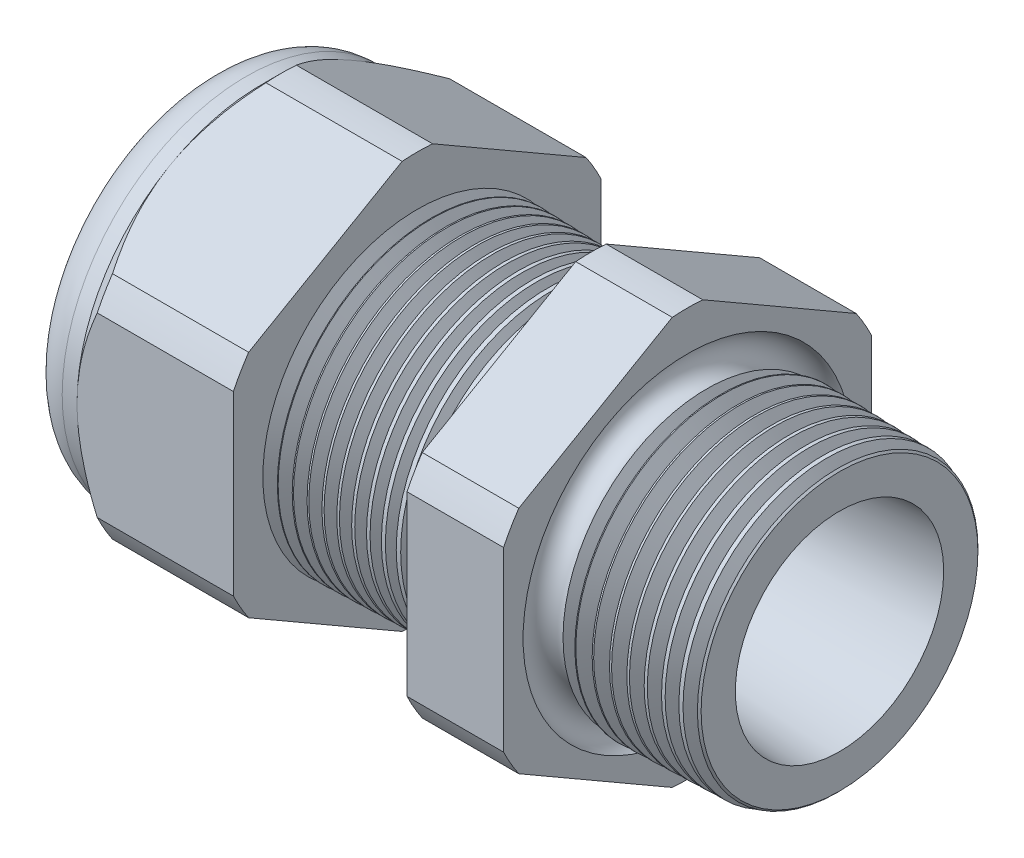
SolidWorks part; units mm, degrees
ref_plane "Front Plane" through (0, 0, 0) normal (0, 0, 1) x (1, 0, 0)
ref_plane "Top Plane" through (0, 0, 0) normal (0, 1, 0) x (1, 0, 0)
ref_plane "Right Plane" through (0, 0, 0) normal (1, 0, 0) x (0, 0, -1)
sketch "Sketch10" plane through (0, 0, 0) normal (0, 0, 1) x (1, 0, 0)
  line L0 (0, 0) -> (-115.3565, 0) construction
  line L1 (-32.766, 3.937) -> (-21.866, 3.937)
  line L2 (0, 5.3964) -> (0, 7.4284)
  line L3 (-7.874, 7.6346) -> (0, 7.4284)
  line L4 (-7.874, 19.05) -> (-7.874, 7.6346)
  line L5 (-7.874, 19.05) -> (-12.874, 19.05)
  line L6 (-12.874, 19.05) -> (-12.874, 7.7655)
  line L7 (-21.866, 8.001) -> (-12.874, 7.7655)
  line L8 (-21.866, 8.001) -> (-21.866, 19.05)
  line L9 (-21.866, 19.05) -> (-29.966, 19.05)
  line L10 (-29.966, 19.05) -> (-29.966, 9.525)
  line L11 (-29.966, 9.525) -> (-32.766, 9.525)
  line L12 (-32.766, 9.525) -> (-32.766, 3.937)
  line L13 (-21.866, 3.937) -> (0, 5.3964)
  dimension "D1" = 32.766
  dimension "D2" = 7.874
  dimension "D3" = 1.5
  dimension "D4" = 2.032
  dimension "A" = 16.002
  dimension "D6" = 19.05
  dimension "D8" = 38.1
  dimension "D9" = 2.8
  dimension "D10" = 8.1
  dimension "D11" = 5
  dimension "D" = 7.874
revolve "Revolve2" add sketch "Sketch10" angle 360 about L0
sketch "Sketch12" plane through (-29.966, 0, 0) normal (-1, 0, 0) x (0, 0, 1)
  line L1 (-0.7885, 10.5433) -> (-8.7365, 5.9545)
  line L2 (-9.525, 4.5888) -> (-9.525, -4.5888)
  line L3 (-8.7365, -5.9545) -> (-0.7885, -10.5433)
  line L4 (0.7885, -10.5433) -> (8.7365, -5.9545)
  line L5 (9.525, -4.5888) -> (9.525, 4.5888)
  line L6 (8.7365, 5.9545) -> (0.7885, 10.5433)
  circle A0 centre (0, 0) radius 9.525 construction
  arc A1 (0.7885, 10.5433) -> (-0.7885, 10.5433) centre (0, 0) ccw
  arc A2 (-8.7365, 5.9545) -> (-9.525, 4.5888) centre (0, 0) ccw
  arc A3 (-9.525, -4.5888) -> (-8.7365, -5.9545) centre (0, 0) ccw
  arc A4 (-0.7885, -10.5433) -> (0.7885, -10.5433) centre (0, 0) ccw
  arc A5 (8.7365, -5.9545) -> (9.525, -4.5888) centre (0, 0) ccw
  arc A6 (9.525, 4.5888) -> (8.7365, 5.9545) centre (0, 0) ccw
  dimension "D2" = 21.1455
  dimension "D1" = 19.05
extrude "Cut-Extrude2" cut sketch "Sketch12" against normal through all flip side to cut
fillet "Fillet4" radius 2.032 1 edges at (-32.766, 0, -9.525)
sketch "Sketch19" plane through (-29.966, 0, 0) normal (-1, 0, 0) x (0, 0, 1)
  line L0 (9.525, 0) -> (9.525, 4.5888) construction
  circle A0 centre (0, 0) radius 9.525
extrude "Cut-Extrude3" cut sketch "Sketch19" against normal blind 2 draft 45 flip side to cut
chamfer "Chamfer1" distance 0.254 angle 45 1 edges at (0, 0, -7.4284)
sketch "Sketch21" plane through (-32.766, 0, 0) normal (-1, 0, 0) x (0, 0, 1)
  circle A0 centre (0, 0) radius 3.937
  circle A2 centre (0, 0) radius 3.937 construction
extrude "plug" add sketch "Sketch21" against normal blind 3.81 separate body
sketch "Sketch22" plane through (-32.766, 0, 0) normal (-1, 0, 0) x (0, 0, 1)
  circle A0 centre (0, 0) radius 3.683
  circle A1 centre (0, 0) radius 3.937 construction
  dimension "D1" = 0.254
extrude "Cut-Extrude4" cut sketch "Sketch22" against normal blind 0.508
sketch "Sketch27" plane through (-32.258, 0, 0) normal (-1, 0, 0) x (0, 0, 1)
  line L0 (-4.3624, 0) -> (4.3624, 0) construction
  circle A0 centre (-2.2804, 0) radius 1.397
  circle A1 centre (0, 0) radius 3.683 construction
  dimension "D1" = 0.0056
  dimension "holedia" = 2.794
extrude "plugholes" cut sketch "Sketch27" against normal through all
pattern_circular "CirPattern1" count 4 over 360 about axis through (0, 0, 0) along (1, 0, 0) of "plugholes"
sketch "Sketch28" [suppressed] plane through (-29.464, 0, 0) normal (-1, 0, 0) x (0, 0, 1)
  circle A0 centre (0, 0) radius 0.762
  dimension "midholedia" = 2.794
extrude "midhole" [suppressed] cut sketch "Sketch28" against normal through all
sketch "Sketch29" plane through (0, 0, 0) normal (0, 0, 1) x (1, 0, 0)
  line L0 (-21.866, 8.001) -> (-21.133, 7.9818)
  line L1 (-12.874, 7.7655) -> (-21.866, 8.001) construction
  line L2 (-21.133, 7.9818) -> (-21.5161, 7.3566)
  line L3 (-21.5161, 7.3566) -> (-21.866, 8.001)
  dimension "D1" = 60
  dimension "D2" = 60
  dimension "D3" = 0.635
revolve "Cut-Revolve1" cut sketch "Sketch29" angle 360 about axis through (0, 0, 0) along (-1, 0, 0)
pattern_linear "LPattern1" count 12 spacing 0.762 along (1, 0, 0) of "Cut-Revolve1"
sketch "Sketch30" plane through (0, 0, 0) normal (0, 0, 1) x (1, 0, 0)
  line L0 (-7.874, 7.6346) -> (-6.9944, 7.6116)
  line L1 (-7.874, 10.5433) -> (-7.874, 5.9545) construction
  line L2 (-0.2539, 7.4351) -> (-7.874, 7.6346) construction
  line L3 (-6.9944, 7.6116) -> (-7.4542, 6.8614)
  line L4 (-7.4542, 6.8614) -> (-7.874, 7.6346)
  dimension "D1" = 60
  dimension "D2" = 60
  dimension "D3" = 0.762
revolve "Cut-Revolve2" cut sketch "Sketch30" angle 360 about axis through (0, 0, 0) along (-1, 0, 0)
pattern_linear "LPattern2" count 9 spacing 0.889 along (1, 0, 0) of "Cut-Revolve2"
sketch "Sketch31" [suppressed] plane through (-38.354, 0, 0) normal (-1, 0, 0) x (0, 0, 1)
  line L0 (-1.905, 1.905) -> (1.905, 1.905)
  line L1 (-1.905, -1.905) -> (1.905, -1.905)
  circle A0 centre (0, 0) radius 1.905 construction
  arc A1 (-1.905, 1.905) -> (-1.905, -1.905) centre (-1.905, 0) ccw
  arc A2 (1.905, 1.905) -> (1.905, -1.905) centre (1.905, 0) cw
extrude "Cut-Extrude5" [suppressed] cut sketch "Sketch31" against normal through all
sketch "Sketch32" plane through (0, 0, 0) normal (0, 0, 1) x (1, 0, 0)
  line L0 (-7.874, 10.5433) -> (-7.874, 5.9545) construction
  circle A0 centre (-7.747, 7.6346) radius 0.889
  dimension "D2" = 1.778
  dimension "D1" = 0.127
revolve "Cut-Revolve3" cut sketch "Sketch32" angle 360 about axis through (0, 0, 0) along (-1, 0, 0)
